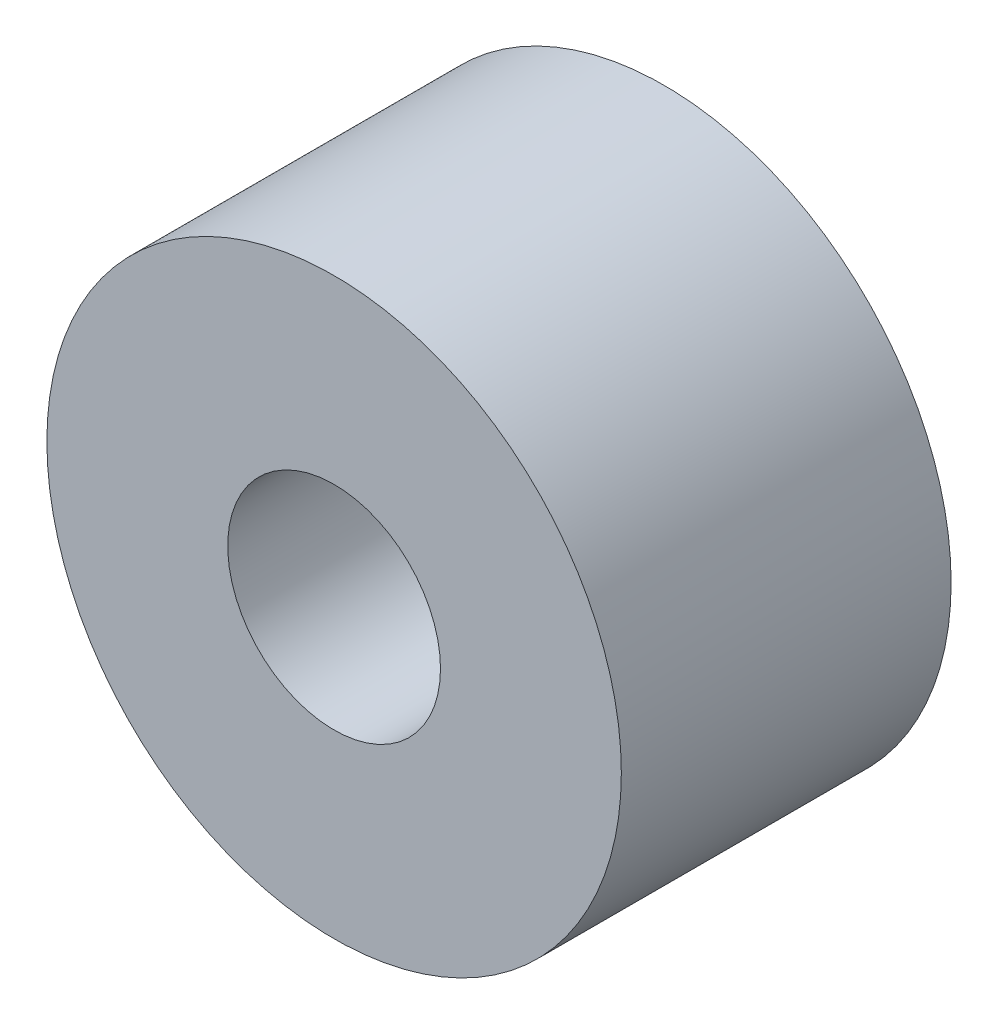
SolidWorks part; units mm, degrees
ref_plane "Front Plane" through (0, 0, 0) normal (0, 0, 1) x (1, 0, 0)
ref_plane "Top Plane" through (0, 0, 0) normal (0, 1, 0) x (1, 0, 0)
ref_plane "Right Plane" through (0, 0, 0) normal (1, 0, 0) x (0, 0, -1)
sketch "Sketch1" plane through (0, 0, 0) normal (0, 0, 1) x (1, 0, 0)
  circle A0 centre (0, 0) radius 8.5725
  circle A1 centre (0, 0) radius 3.175
  dimension "D1" = 17.145
  dimension "D2" = 6.35
extrude "Boss-Extrude1" add sketch "Sketch1" along normal blind 9.8425
